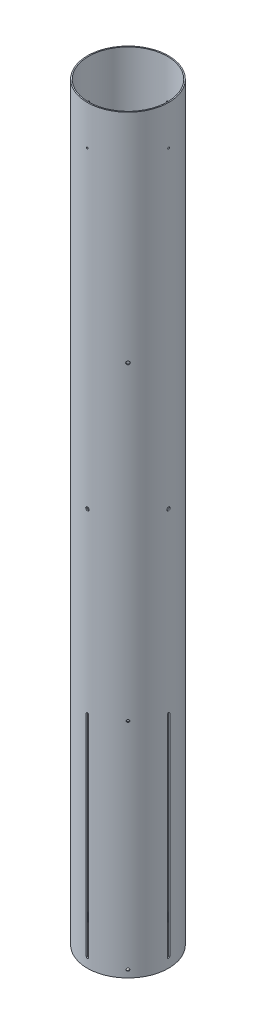
SolidWorks part; units mm, degrees
ref_plane "Front Plane" through (0, 0, 0) normal (0, 0, 1) x (1, 0, 0)
ref_plane "Top Plane" through (0, 0, 0) normal (0, 1, 0) x (1, 0, 0)
ref_plane "Right Plane" through (0, 0, 0) normal (1, 0, 0) x (0, 0, -1)
sketch "Sustainer Tube Profile" plane through (0, 0, 0) normal (0, 1, 0) x (1, 0, 0)
  circle A0 centre (0, 0) radius 76.2
  circle A1 centre (0, 0) radius 78.359
  dimension "D1" = 152.4
  dimension "D2" = 156.718
extrude "Sustainer Tube Body" add sketch "Sustainer Tube Profile" along normal blind 1447.8
ref_plane "Plane1" through (0, 0, 78.359) normal (0, 0, 1) x (1, 0, 0)
ref_plane "Plane3" through (0, 0, 0) normal (0.7071, 0, 0.7071) x (0, -1, 0)
sketch "Fin Slot Profile" plane through (0, 0, 78.359) normal (0, 0, 1) x (1, 0, 0)
  line L0 (0, 0) -> (0, 1447.8) construction
  line L5 (76.2, 1447.8) -> (-76.2, 1447.8) construction
  line L6 (-78.359, 0) -> (78.359, 0) construction
  line L7 (2.3813, 19.05) -> (-2.3813, 19.05)
  line L8 (0, 19.05) -> (0, 425.45)
  line L9 (2.3813, 425.45) -> (-2.3813, 425.45)
  line L10 (-2.3813, 19.05) -> (-2.3813, 425.45)
  line L11 (2.3813, 19.05) -> (2.3813, 425.45)
  arc A0 (-2.3813, 19.05) -> (2.3812, 19.05) centre (0, 19.05) ccw
  arc A1 (2.3813, 425.45) -> (-2.3812, 425.45) centre (0, 425.45) ccw
  dimension "D1" = 406.4
  dimension "D2" = 19.05
  dimension "D3" = 2.3813
extrude "Fin Slot Cut" cut sketch "Fin Slot Profile" against normal up to surface (2.1962 mm away) contours L7 L11 L9 L8 | L10 L7 L8 L9 | L0 L9 A1 | L9 L0 A1 | A0 L0 L7 | L0 A0 L7
pattern_circular "Fin Slot Pattern" count 4 over 360 about axis through (0, 0, 0) along (0, 1, 0) of "Fin Slot Cut"
sketch "Sketch1" plane through (0, 0, 0) normal (0, 0, 1) x (1, 0, 0)
  line L0 (76.2, 1447.8) -> (-76.2, 1447.8) construction
  circle A0 centre (0, 1371.6) radius 1.143
  dimension "D1" = 2.286
  dimension "D2" = 76.2
extrude "Cut-Extrude1" [suppressed] cut sketch "Sketch1" against normal through all both and the other way through all
pattern_circular "CirPattern1" [suppressed] count 4 over 360
sketch "Sketch2" plane through (0, 0, 0) normal (0.7071, 0, 0.7071) x (0.7071, 0, -0.7071)
  line L0 (76.2, 1447.8) -> (-76.2, 1447.8) construction
  circle A0 centre (0, 1028.7) radius 3.175
  dimension "D2" = 419.1
extrude "Vent Hole" cut sketch "Sketch2" along normal through all
sketch "Sketch3" plane through (0, 0, 0) normal (0, 0, 1) x (1, 0, 0)
  line L0 (78.359, 1447.8) -> (-78.359, 1447.8) construction
  circle A0 centre (0, 768.35) radius 3.2639
  dimension "D2" = 6.5278
  dimension "D1" = 679.45
extrude "Cut-Extrude3" cut sketch "Sketch3" against normal through all both and the other way through all
pattern_circular "CirPattern2" count 4 over 360 about axis through (0, 1447.8, 0) along (0, 1, 0) of "Cut-Extrude3"
ref_plane "Plane2" through (55.4082, 0, 55.4082) normal (0.7071, 0, 0.7071) x (0, -1, 0)
sketch "Sketch4" plane through (55.4082, 0, 55.4082) normal (0.7071, 0, 0.7071) x (0, -1, 0)
  circle A0 centre (-14.0462, 0) radius 2.5794
  circle A1 centre (-429.9255, 0) radius 2.5794
  dimension "D1" = 5.1587
  dimension "D2" = 14.0462
  dimension "D3" = 429.9255
extrude "Cut-Extrude4" cut sketch "Sketch4" against normal up to surface and the other way through all up to face at (-76.1337, 767.6026, 3.1772)
ref_plane "Plane6" through (-78.359, 0, 0) normal (-1, 0, 0) x (0, 0, 1)
ref_plane "Plane5" through (-55.4082, 0, -55.4082) normal (-0.7071, 0, -0.7071) x (-0.7071, 0, 0.7071)
sketch "Sketch9" plane through (-78.359, 0, 0) normal (1, 0, 0) x (0, 0, -1)
  line L0 (78.359, 1447.8) -> (-78.359, 1447.8) construction
  point P0 (0, 1371.6)
  dimension "D1" = 76.2
hole_wizard "#4 Clearance Hole1" positions "Sketch9" profile "Sketch10" hole size "#4" standard "ANSI Inch"
sketch "Sketch10" plane through (-78.359, 1371.6, 0) normal (0, 1, 0) x (0, 0, 1)
  line L0 (0, 0) -> (0, 5.8066)
  line L1 (0, 5.8066) -> (1.6319, 4.826)
  line L2 (1.6319, 4.826) -> (1.6319, 0)
  line L5 (1.6319, 0) -> (0, 0)
  line L10 (0, 5.8066) -> (-1.6319, 4.826) construction
  line L11 (0, -6.35) -> (0, 107.95) construction
  dimension "Hole Dia." = 3.2639
  dimension "Hole Depth" = 4.826
  dimension "Drill Angle" = 118
pattern_circular "CirPattern3" count 4 every 90 about axis through (0, 1447.8, 0) along (0, 1, 0) of "#4 Clearance Hole1"
equation "\"Length\"= 57"
equation "\"Outer Diameter\"= 6.17"
equation "\"Inner Diameter\"= 6"
equation "\"Wall Thickness\"= 0.085"
equation "\"D1@Sustainer Tube Profile\" = \"Inner Diameter\""
equation "\"D2@Sustainer Tube Profile\" = \"Outer Diameter\""
equation "\"D1@Sustainer Tube Body\" = \"Length\""
equation "\"Root Chord\"= 16"
equation "\"Fin Offset\"= 3 / 4"
equation "\"D1@Fin Slot Profile\"=\"Root Chord\" "
equation "\"D2@Fin Slot Profile\" = \"Fin Offset\""
equation "\"Fin Thickness\"= ( 3 / 16 ) / 2"
equation "\"D3@Fin Slot Profile\"=\"Fin Thickness\""
equation "\"Shear Pin Dia\"= 3 / 32"
equation "\"Shear Pin Offset\"= 3"
equation "\"Bulkhead Screw Dia\"= 0.257"
equation "\"Bulkhead Screw Offset\"= 26.75"
equation "\"Rail Button Dia\"= 0.2031"
equation "\"Rail Button Aft Offset\"= 0.553"
equation "\"Rail Button Forward Offset\" = 16.926200785"
equation "\"Vent Hole Dia\"= 1 / 4"
equation "\"Vent Hole Offset\"= 16.5"
equation "\"D1@Sketch2\"=\"Vent Hole Dia\""
equation "\"D2@Sketch2\"=\"Vent Hole Offset\""
equation "\"D1@Sketch3\"=\"Bulkhead Screw Offset\""
equation "\"D2@Sketch3\"=\"Bulkhead Screw Dia\""
equation "\"D1@Sketch4\"=\"Rail Button Dia\""
equation "\"D2@Sketch4\"=\"Rail Button Aft Offset\""
equation "\"D3@Sketch4\"=\"Rail Button Forward Offset\""
equation "\"D1@Sketch9\"=\"Shear Pin Offset\""
